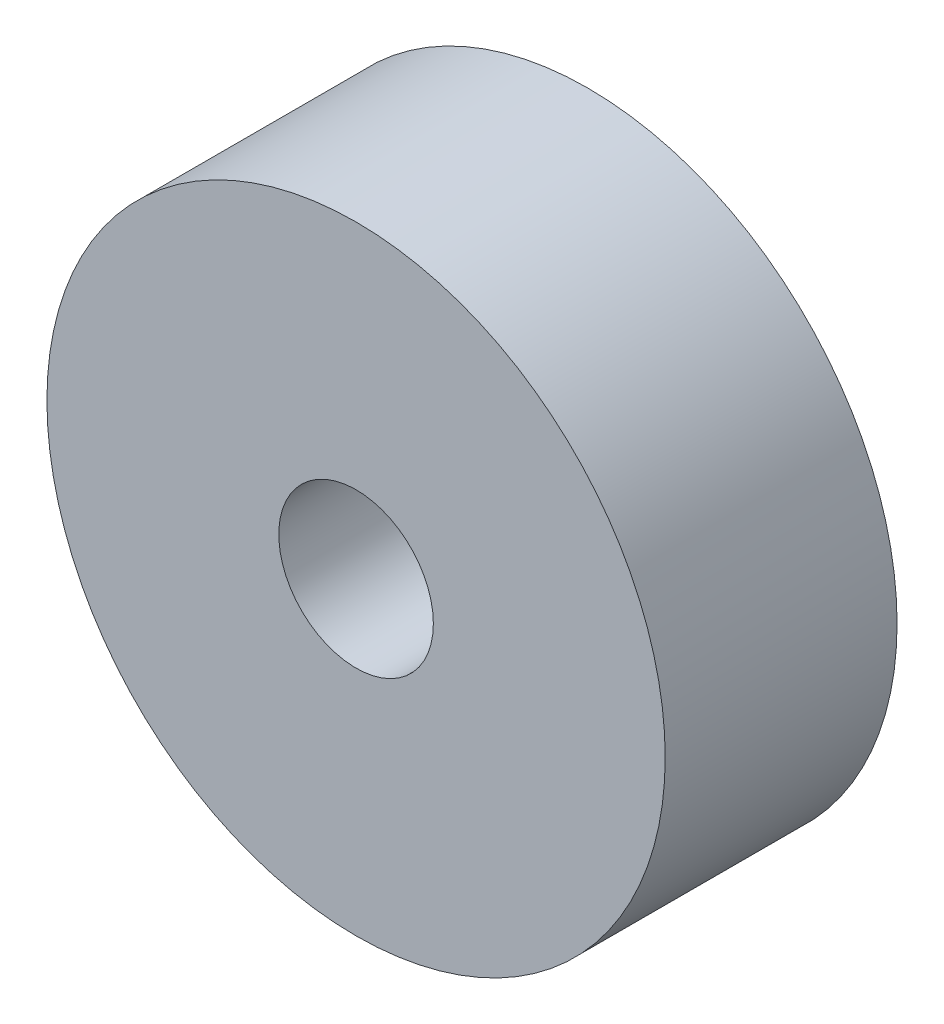
SolidWorks part; units mm, degrees
ref_plane "前视基准面" through (0, 0, 0) normal (0, 0, 1) x (1, 0, 0)
ref_plane "上视基准面" through (0, 0, 0) normal (0, 1, 0) x (1, 0, 0)
ref_plane "右视基准面" through (0, 0, 0) normal (1, 0, 0) x (0, 0, -1)
other "Configuration Table"
sketch "草图1" plane through (0, 0, 0) normal (0, 0, 1) x (1, 0, 0)
  circle A0 centre (0, 0) radius 2
  circle A1 centre (0, 0) radius 8
extrude "凸台-拉伸1" add sketch "草图1" along normal blind 6
